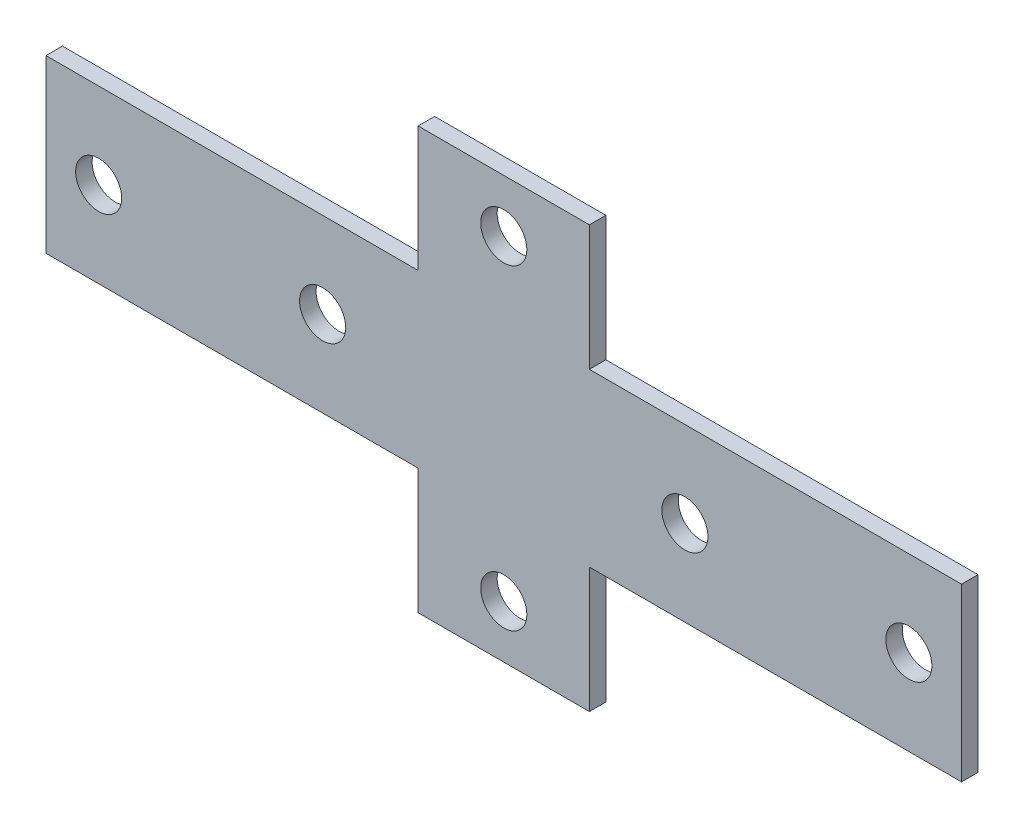
SolidWorks part; units mm, degrees
ref_plane "Спереди" through (0, 0, 0) normal (0, 0, 1) x (1, 0, 0)
ref_plane "Сверху" through (0, 0, 0) normal (0, 1, 0) x (1, 0, 0)
ref_plane "Справа" through (0, 0, 0) normal (1, 0, 0) x (0, 0, -1)
sketch "Эскиз1" plane through (0, 0, 0) normal (0, 0, 1) x (1, 0, 0)
  line L0 (13, -13) -> (69.5, -13)
  line L1 (-69.5, 13) -> (-13, 13)
  line L2 (-69.5, 13) -> (-69.5, -13)
  line L3 (-69.5, -13) -> (-13, -13)
  line L4 (69.5, 13) -> (69.5, -13)
  line L5 (-69.5, 13) -> (69.5, -13) construction
  line L6 (-69.5, -13) -> (69.5, 13) construction
  line L7 (-13, -32) -> (13, -32)
  line L8 (-13, -32) -> (-13, -13)
  line L9 (-13, 32) -> (13, 32)
  line L10 (13, -32) -> (13, -13)
  line L11 (-13, -32) -> (13, 32) construction
  line L12 (-13, 32) -> (13, -32) construction
  line L13 (13, 13) -> (69.5, 13)
  line L14 (-13, 13) -> (-13, 32)
  line L15 (13, 13) -> (13, 32)
  line L16 (0, 24) -> (0, -24) construction
  line L17 (0, 24) -> (0, 32) construction
  line L18 (-61.5, 0) -> (-69.5, 0) construction
  circle A0 centre (0, 24) radius 3.5
  circle A1 centre (0, -24) radius 3.5
  circle A2 centre (-61.5, 0) radius 3.5
  circle A3 centre (-27.5, 0) radius 3.5
  circle A4 centre (27.5, 0) radius 3.5
  circle A5 centre (61.5, 0) radius 3.5
  point P0 (0, 0)
  point P6 (0, 0)
  dimension "D4" = 8
  dimension "D5" = 7
  dimension "D6" = 34
  dimension "D1" = 139
  dimension "D2" = 64
  dimension "D3" = 26
extrude "Бобышка-Вытянуть1" add sketch "Эскиз1" along normal blind 2.5
